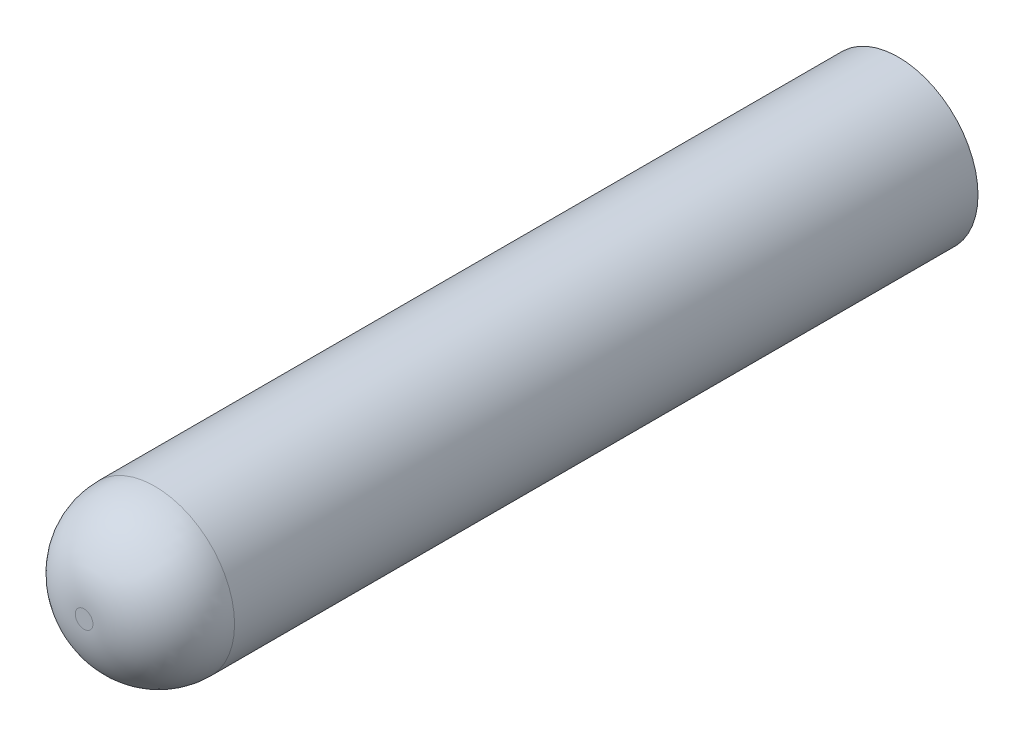
SolidWorks part; units mm, degrees
ref_plane "Front Plane" through (0, 0, 0) normal (0, 0, 1) x (1, 0, 0)
ref_plane "Top Plane" through (0, 0, 0) normal (0, 1, 0) x (1, 0, 0)
ref_plane "Right Plane" through (0, 0, 0) normal (1, 0, 0) x (0, 0, -1)
sketch "草图1" plane through (0, 0, 0) normal (0, 0, 1) x (1, 0, 0)
  circle A0 centre (0, 0) radius 2.25
  dimension "D1" = 4.5
extrude "凸台-拉伸2" add sketch "草图1" along normal blind 23
sketch "草图7" plane through (0, 0, 0) normal (0, 0, 1) x (1, 0, 0)
  line L1 (1.175, -1.175) -> (-1.175, -1.175)
  line L2 (1.175, -1.175) -> (1.175, 1.175)
  line L3 (1.175, 1.175) -> (-1.175, 1.175)
  line L4 (-1.175, -1.175) -> (-1.175, 1.175)
  line L5 (1.175, -1.175) -> (-1.175, 1.175) construction
  line L6 (1.175, 1.175) -> (-1.175, -1.175) construction
  point P0 (0, 0)
  dimension "D1" = 2.35
  dimension "D2" = 2.35
extrude "切除-拉伸3" cut sketch "草图7" along normal blind 4.5 from surface at 0 starting at face at (2.25, 0, 0)
fillet "圆角2" radius 2 1 edges at (2.25, 0, 23)
